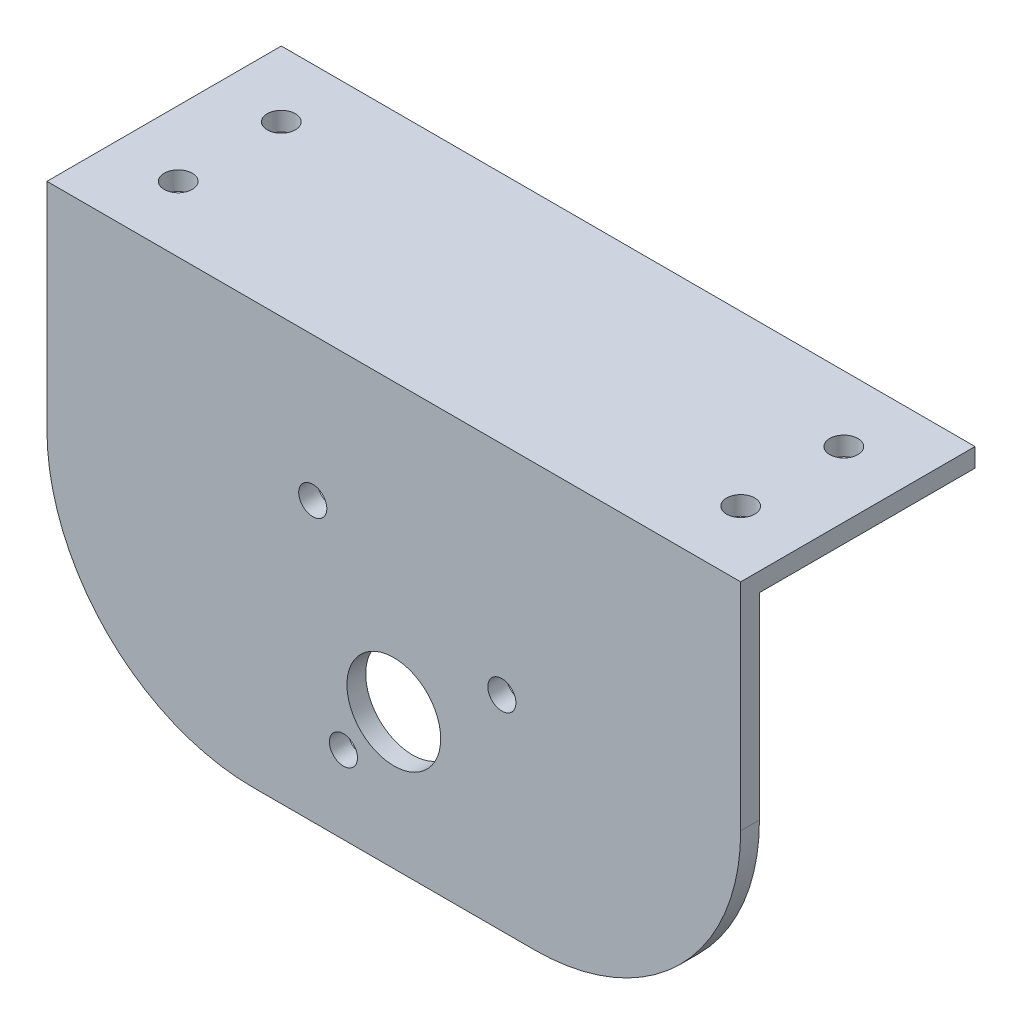
SolidWorks part; units mm, degrees
ref_plane "Спереди" through (0, 0, 0) normal (0, 0, 1) x (1, 0, 0)
ref_plane "Сверху" through (0, 0, 0) normal (0, 1, 0) x (1, 0, 0)
ref_plane "Справа" through (0, 0, 0) normal (1, 0, 0) x (0, 0, -1)
sketch "Эскиз1" plane through (0, 0, 0) normal (0, 1, 0) x (1, 0, 0)
  line L1 (0, 0) -> (74, 0)
  line L2 (0, 0) -> (0, 25)
  line L3 (0, 25) -> (74, 25)
  line L4 (74, 0) -> (74, 25)
  circle A0 centre (7, 18) radius 1.5
  circle A1 centre (67, 18) radius 1.5
  circle A2 centre (7, 7) radius 1.5
  circle A3 centre (67, 7) radius 1.5
  dimension "D3" = 7
  dimension "D4" = 7
  dimension "D5" = 7
  dimension "D6" = 7
  dimension "D7" = 3
  dimension "D8" = 18
  dimension "D9" = 18
  dimension "D1" = 74
  dimension "D2" = 25
extrude "Бобышка-Вытянуть1" add sketch "Эскиз1" along normal blind 2
sketch "Эскиз2" plane through (0, 0, 0) normal (0, 0, 1) x (1, 0, 0)
  line L0 (37, -43) -> (37, 2) construction
  line L1 (0, 2) -> (74, 2)
  line L2 (0, 2) -> (0, -21)
  line L3 (22, -43) -> (52, -43)
  line L4 (74, 2) -> (74, -21)
  line L5 (0, 2) -> (74, 2) construction
  line L7 (37, -28.5) -> (55.9461, -28.5) construction
  circle A0 centre (37, -28.5) radius 5
  arc A1 (52, -43) -> (74, -21) centre (52, -21) ccw
  arc A2 (0, -21) -> (22, -43) centre (22, -21) ccw
  circle A3 centre (28.3542, -13.307) radius 1.5
  circle A4 centre (48.525, -21.1738) radius 1.5
  circle A5 centre (31.6268, -34.7088) radius 1.5
  dimension "D3" = 10
  dimension "D4" = 22
  dimension "D1" = 45
  dimension "D2" = 30.5
extrude "Бобышка-Вытянуть2" add sketch "Эскиз2" against normal blind 2
